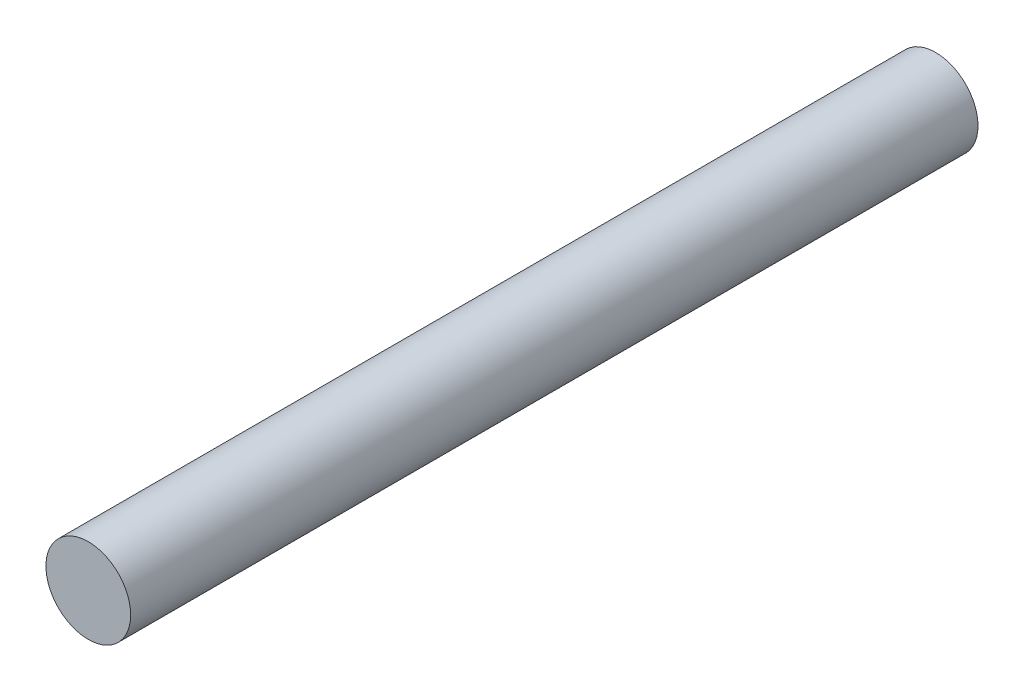
SolidWorks part; units mm, degrees
material "不锈钢 (铁素体)"
ref_plane "前视基准面" through (0, 0, 0) normal (0, 0, 1) x (1, 0, 0)
ref_plane "上视基准面" through (0, 0, 0) normal (0, 1, 0) x (1, 0, 0)
ref_plane "右视基准面" through (0, 0, 0) normal (1, 0, 0) x (0, 0, -1)
sketch "草图1" plane through (0, 0, 0) normal (0, 0, 1) x (1, 0, 0)
  circle A0 centre (0, 0) radius 1.5
extrude "凸台-拉伸1" add sketch "草图1" along normal blind 30
